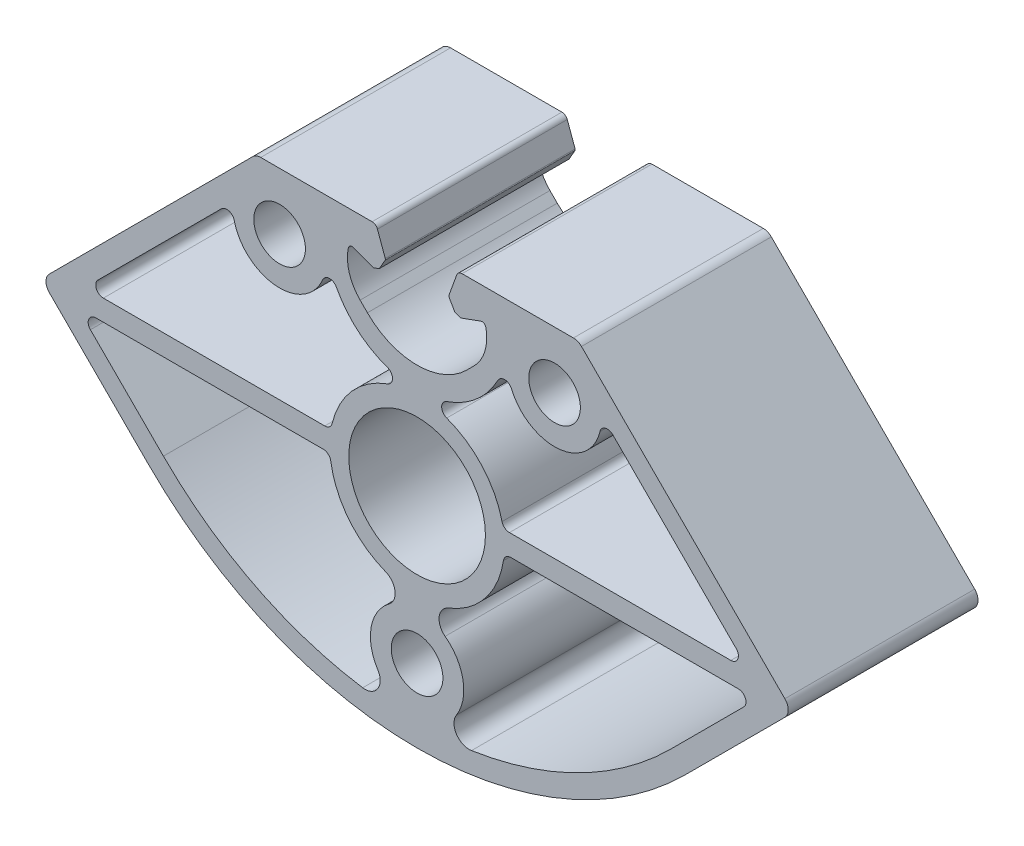
SolidWorks part; units mm, degrees
material "6005-T5"
ref_plane "Front" through (0, 0, 0) normal (0, 0, 1) x (1, 0, 0)
ref_plane "Top" through (0, 0, 0) normal (0, 1, 0) x (1, 0, 0)
ref_plane "Right" through (0, 0, 0) normal (1, 0, 0) x (0, 0, -1)
sketch "Sk Main Extrusion" plane through (0, 0, 0) normal (0, 0, 1) x (1, 0, 0)
  line L30 (33.4108, -12.1819) -> (43.0256, -2.5671)
  line L31 (42.3184, -0.86) -> (12.3608, -0.86)
  line L32 (-12.3608, -0.86) -> (-42.3184, -0.86)
  line L33 (-43.0256, -2.5671) -> (-33.4108, -12.1819)
  line L34 (42.027, 3.5971) -> (25.77, 19.8541)
  line L35 (12.1613, 1.89) -> (41.3199, 1.89)
  line L36 (-25.77, 19.8541) -> (-42.027, 3.5971)
  line L37 (-41.3199, 1.89) -> (-12.1613, 1.89)
  line L38 (5.2221, 27.8065) -> (4.1901, 24.9712)
  line L39 (4.2085, 24.7607) -> (4.9876, 23.4113)
  line L40 (4.9876, 23.4113) -> (5.7185, 23.1453)
  line L41 (5.7185, 23.1453) -> (8.3962, 24.1198)
  line L42 (7.5042, 18.5727) -> (6.5407, 17.6093)
  line L43 (-6.5407, 17.6093) -> (-7.5042, 18.5727)
  line L44 (-8.3962, 24.1198) -> (-5.7185, 23.1453)
  line L45 (-5.7185, 23.1453) -> (-4.9876, 23.4113)
  line L46 (-4.9876, 23.4113) -> (-4.2085, 24.7607)
  line L47 (-4.1901, 24.9712) -> (-5.2221, 27.8065)
  line L48 (-5.9268, 28.3) -> (-20.5919, 28.3)
  line L49 (-21.6525, 27.8607) -> (-48.4368, 1.0764)
  line L50 (-48.4368, -1.0449) -> (-35.3553, -14.1264)
  line L51 (35.3553, -14.1264) -> (48.4368, -1.0449)
  line L52 (48.4368, 1.0764) -> (21.6525, 27.8607)
  line L53 (20.5919, 28.3) -> (5.9268, 28.3)
  arc A48 (43.0256, -2.5671) -> (42.3184, -0.86) centre (42.3184, -1.86) ccw
  arc A49 (12.3608, -0.86) -> (11.372, -1.7112) centre (12.3608, -1.86) ccw
  arc A50 (4.168, -10.7181) -> (11.372, -1.7112) centre (0, 0) ccw
  arc A51 (4.168, -10.7181) -> (3.6921, -14.1816) centre (4.8928, -12.5821) ccw
  arc A52 (5.1778, -22.4186) -> (3.6921, -14.1816) centre (0, -19.1) ccw
  arc A53 (5.1778, -22.4186) -> (7.1649, -25.4747) centre (6.8616, -23.4978) ccw
  arc A54 (7.1649, -25.4747) -> (33.4108, -12.1819) centre (0, 21.2289) ccw
  arc A55 (5.9268, 28.3) -> (5.2221, 27.8065) centre (5.9268, 27.55) ccw
  arc A56 (4.1901, 24.9712) -> (4.2085, 24.7607) centre (4.425, 24.8857) ccw
  arc A57 (9.057, 23.7507) -> (8.3962, 24.1198) centre (8.5672, 23.65) ccw
  arc A58 (7.5042, 18.5727) -> (9.057, 23.7507) centre (3.4737, 22.6032) ccw
  arc A59 (-6.5407, 17.6093) -> (6.5407, 17.6093) centre (0, 24.15) ccw
  arc A60 (-9.057, 23.7507) -> (-7.5042, 18.5727) centre (-3.4737, 22.6032) ccw
  arc A61 (-8.3962, 24.1198) -> (-9.057, 23.7507) centre (-8.5672, 23.65) ccw
  arc A62 (-4.2085, 24.7607) -> (-4.1901, 24.9712) centre (-4.425, 24.8857) ccw
  arc A63 (-5.2221, 27.8065) -> (-5.9268, 28.3) centre (-5.9268, 27.55) ccw
  arc A64 (-20.5919, 28.3) -> (-21.6525, 27.8607) centre (-20.5919, 26.8) ccw
  arc A65 (-48.4368, 1.0764) -> (-48.4368, -1.0449) centre (-47.3762, 0.0157) ccw
  arc A66 (-35.3553, -14.1264) -> (35.3553, -14.1264) centre (0, 21.2289) ccw
  arc A67 (48.4368, -1.0449) -> (48.4368, 1.0764) centre (47.3762, 0.0157) ccw
  arc A68 (21.6525, 27.8607) -> (20.5919, 28.3) centre (20.5919, 26.8) ccw
  arc A69 (-3.6921, -14.1816) -> (-4.168, -10.7181) centre (-4.8928, -12.5821) ccw
  arc A70 (-11.372, -1.7112) -> (-4.168, -10.7181) centre (0, 0) ccw
  arc A71 (-11.372, -1.7112) -> (-12.3608, -0.86) centre (-12.3608, -1.86) ccw
  arc A72 (-42.3184, -0.86) -> (-43.0256, -2.5671) centre (-42.3184, -1.86) ccw
  arc A73 (-33.4108, -12.1819) -> (-7.1649, -25.4747) centre (0, 21.2289) ccw
  arc A74 (-7.1649, -25.4747) -> (-5.1778, -22.4186) centre (-6.8616, -23.4978) ccw
  arc A75 (-3.6921, -14.1816) -> (-5.1778, -22.4186) centre (0, -19.1) ccw
  arc A76 (41.3199, 1.89) -> (42.027, 3.5971) centre (41.3199, 2.89) ccw
  arc A77 (25.77, 19.8541) -> (24.09, 19.3782) centre (25.0629, 19.147) ccw
  arc A78 (12.4396, 18.4109) -> (24.09, 19.3782) centre (18.1066, 20.8) ccw
  arc A79 (12.4396, 18.4109) -> (10.6322, 18.4861) centre (11.5182, 18.0224) ccw
  arc A80 (3.9113, 12.7053) -> (10.6322, 18.4861) centre (0, 24.05) ccw
  arc A81 (3.9113, 12.7053) -> (3.8983, 10.8191) centre (4.2372, 11.7599) ccw
  arc A82 (11.1884, 2.6588) -> (3.8983, 10.8191) centre (0, 0) ccw
  arc A83 (11.1884, 2.6588) -> (12.1613, 1.89) centre (12.1613, 2.89) ccw
  arc A84 (-12.1613, 1.89) -> (-11.1884, 2.6588) centre (-12.1613, 2.89) ccw
  arc A85 (-3.8983, 10.8191) -> (-11.1884, 2.6588) centre (0, 0) ccw
  arc A86 (-3.8983, 10.8191) -> (-3.9113, 12.7053) centre (-4.2372, 11.7599) ccw
  arc A87 (-10.6322, 18.4861) -> (-3.9113, 12.7053) centre (0, 24.05) ccw
  arc A88 (-10.6322, 18.4861) -> (-12.4396, 18.4109) centre (-11.5182, 18.0224) ccw
  arc A89 (-24.09, 19.3782) -> (-12.4396, 18.4109) centre (-18.1066, 20.8) ccw
  arc A90 (-24.09, 19.3782) -> (-25.77, 19.8541) centre (-25.0629, 19.147) ccw
  arc A91 (-42.027, 3.5971) -> (-41.3199, 1.89) centre (-41.3199, 2.89) ccw
  circle A92 centre (-18.1066, 20.8) radius 3.4
  circle A93 centre (18.1066, 20.8) radius 3.4
  circle A94 centre (0, 0) radius 9
  circle A95 centre (0, -19.1) radius 3.4
  point P120 (0, 28.3)
extrude "Main Extrusion" add sketch "Sk Main Extrusion" against normal blind 25
sketch "Threaded Insert Mate Sketch" plane through (0, 0, 0) normal (0, 0, 1) x (1, 0, 0)
  line L1 (20.5919, 28.3) -> (5.9268, 28.3) construction
  circle A0 centre (0, 21) radius 5.6515
  dimension "D2" = 11.303
  dimension "D1" = 7.3
equation "\"Weight kg\"= round ( \"SW-Mass\" , 2 )"
equation "\"Weight lbs\"= round ( \"SW-Mass\" * 2.2046 , 2 )"
equation "\"Length mm\"= round ( \"Length@Main Extrusion\" , 2 )"
equation "\"Length in\"= round ( \"Length@Main Extrusion\" / 25.4 , 3 )"
